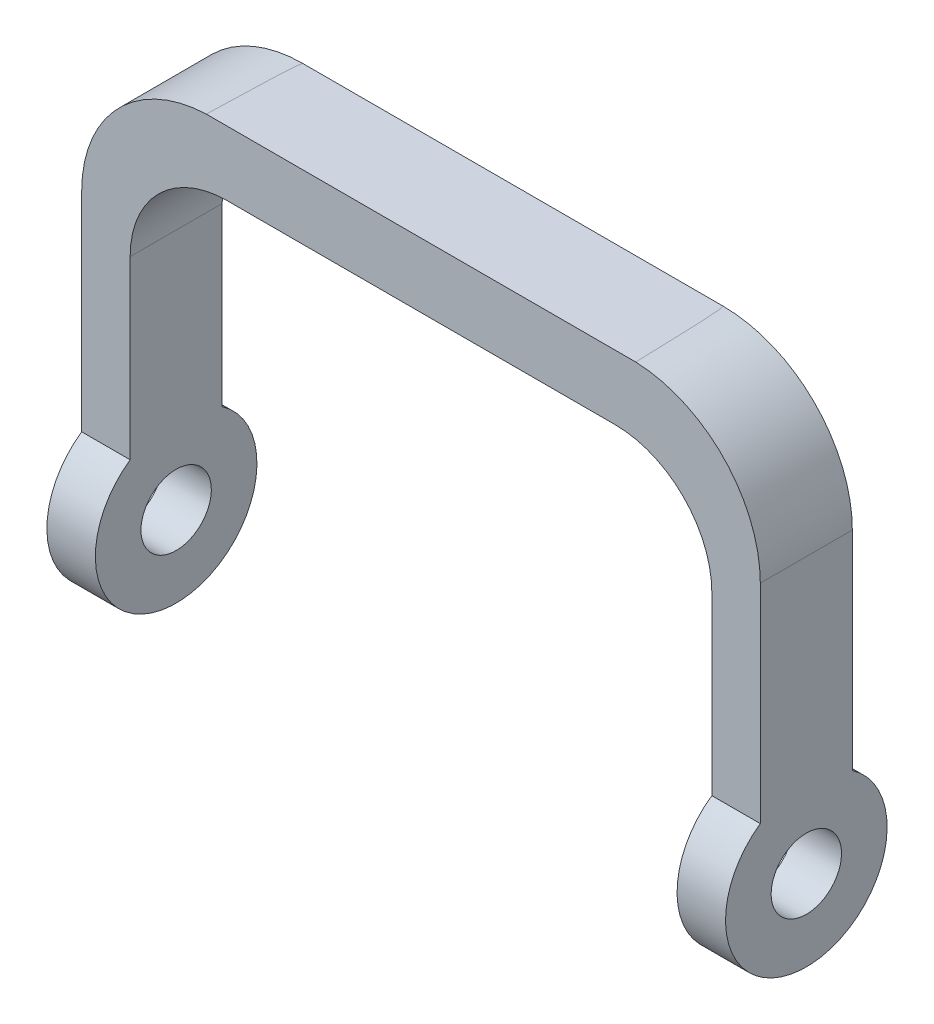
SolidWorks part; units mm, degrees
ref_plane "Спереди" through (0, 0, 0) normal (0, 0, 1) x (1, 0, 0)
ref_plane "Сверху" through (0, 0, 0) normal (0, 1, 0) x (1, 0, 0)
ref_plane "Справа" through (0, 0, 0) normal (1, 0, 0) x (0, 0, -1)
sketch "Эскиз1" plane through (0, 0, 0) normal (0, 0, 1) x (1, 0, 0)
  line L0 (-210, 0) -> (210, 0)
  line L1 (-210, 0) -> (-210, 220)
  line L2 (-130, 300) -> (130, 300)
  line L3 (210, 220) -> (210, 0)
  arc A0 (130, 300) -> (210, 220) centre (130, 220) cw
  arc A1 (-210, 220) -> (-130, 300) centre (-130, 220) cw
  point P4 (0, 0)
  point P11 (-210, 300)
  dimension "D3" = 80
  dimension "D1" = 420
  dimension "D2" = 300
extrude "Бобышка-Вытянуть1" add sketch "Эскиз1" along normal blind 100
sketch "Эскиз2" plane through (0, 0, 100) normal (0, 0, 1) x (1, 0, 0)
  line L0 (-180, 0) -> (180, 0)
  line L1 (-210, 0) -> (210, 0) construction
  line L2 (180, 0) -> (180, 200)
  line L3 (120, 260) -> (-120, 260)
  line L4 (-180, 200) -> (-180, 0)
  arc A0 (180, 200) -> (120, 260) centre (120, 200) ccw
  arc A1 (-120, 260) -> (-180, 200) centre (-120, 200) ccw
  point P6 (0, 0)
  dimension "D1" = 60
  dimension "D2" = 260
  dimension "D3" = 360
extrude "Вырез-Вытянуть1" cut sketch "Эскиз2" against normal through all
sketch "Эскиз3" plane through (210, 0, 0) normal (1, 0, 0) x (0, 0, -1)
  line L0 (-78.4698, 299.9479) -> (-21.5302, 300)
  line L1 (-100, 300) -> (0, 300) construction
  line L2 (-21.5302, 300) -> (-21.5302, 91.1032)
  line L3 (-78.4698, 299.9479) -> (-78.4698, 91.1032)
  arc A1 (-78.4698, 91.1032) -> (-21.5302, 91.1032) centre (-50, 50) ccw
  circle A2 centre (-50, 50) radius 21.7702
extrude "Вырез-Вытянуть2" cut sketch "Эскиз3" against normal through all flip side to cut
